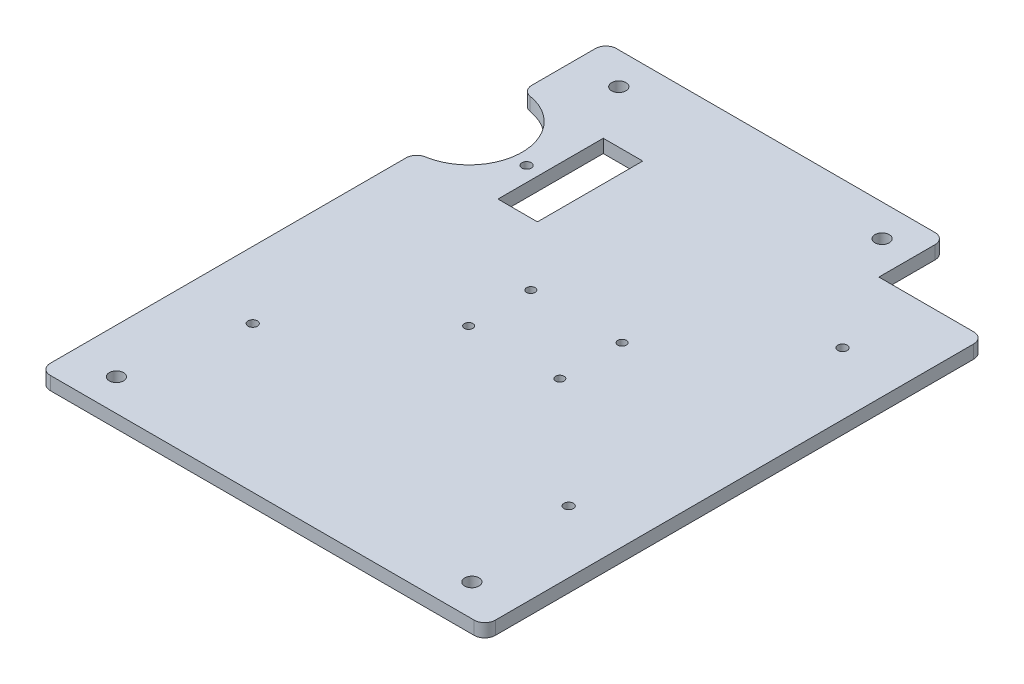
SolidWorks part; units mm, degrees
ref_plane "Front Plane" through (0, 0, 0) normal (0, 0, 1) x (1, 0, 0)
ref_plane "Top Plane" through (0, 0, 0) normal (0, 1, 0) x (1, 0, 0)
ref_plane "Right Plane" through (0, 0, 0) normal (1, 0, 0) x (0, 0, -1)
sketch "Sketch1" plane through (0, 0, 0) normal (0, 1, 0) x (1, 0, 0)
  line L0 (10.795, 128.8415) -> (96.52, 128.8415) construction
  line L1 (0, 136.525) -> (107.315, 136.525) construction
  line L2 (0, 136.525) -> (0, 0)
  line L3 (0, 0) -> (107.315, 0)
  line L4 (107.315, 136.525) -> (107.315, 0) construction
  line L5 (10.795, 7.6835) -> (96.52, 7.6835) construction
  line L6 (53.6575, 136.525) -> (53.6575, 128.8415) construction
  line L7 (0, 68.2625) -> (107.315, 68.2625) construction
  line L8 (53.6575, 7.6835) -> (53.6575, 0) construction
  line L9 (0, 136.525) -> (81.915, 136.525)
  line L10 (81.915, 136.525) -> (81.915, 120.4468)
  line L11 (81.915, 120.4468) -> (107.315, 120.4468)
  line L12 (107.315, 120.4468) -> (107.315, 0)
  circle A0 centre (10.795, 128.8415) radius 1.7272
  circle A2 centre (96.52, 7.6835) radius 1.7272
  circle A3 centre (10.795, 7.6835) radius 1.7272
  circle A4 centre (74.295, 128.8415) radius 1.7272
  dimension "D4" = 3.4544
  dimension "D1" = 107.315
  dimension "D2" = 136.525
  dimension "D3" = 85.725
  dimension "D5" = 7.6835
  dimension "D6" = 22.225
  dimension "D7" = 81.915
  dimension "D8" = 16.0782
extrude "Boss-Extrude1" add sketch "Sketch1" along normal blind 3.2004
sketch "Sketch2" plane through (0, 3.2004, 0) normal (0, 1, 0) x (1, 0, 0)
  line L0 (0, 136.525) -> (0, 0) construction
  line L3 (81.915, 136.525) -> (0, 136.525) construction
  line L4 (24.4475, 103.505) -> (0, 103.505) construction
  line L5 (29.21, 116.205) -> (19.685, 116.205)
  line L6 (29.21, 116.205) -> (29.21, 90.805)
  line L7 (29.21, 90.805) -> (19.685, 90.805)
  line L8 (19.685, 116.205) -> (19.685, 90.805)
  line L9 (24.4475, 116.205) -> (24.4475, 90.805) construction
  line L12 (0, 116.3304) -> (0, 90.6796)
  arc A0 (0, 116.3304) -> (0, 90.6796) centre (0, 103.505) cw
  dimension "D3" = 12.8254
  dimension "D1" = 33.02
  dimension "D4" = 24.4475
  dimension "D5" = 9.525
  dimension "D6" = 25.4
extrude "Cut-Extrude1" cut sketch "Sketch2" against normal up to surface (3.2004 mm away) up to face at (96.52, 0, -5.9563)
sketch "Sketch3" plane through (0, 3.2004, 0) normal (0, 1, 0) x (1, 0, 0)
  line L8 (53.6575, 136.525) -> (53.6575, 0) construction
  line L12 (0, 0) -> (107.315, 0) construction
  line L13 (0, 136.525) -> (107.315, 136.525) construction
  line L74 (92.3128, 101.2825) -> (92.3128, 35.2425) construction
  line L76 (16.1128, 35.2425) -> (16.1128, 101.2825) construction
  line L78 (92.3128, 68.2625) -> (16.1128, 68.2625) construction
  circle A0 centre (92.3128, 101.2825) radius 1.1303
  circle A1 centre (92.3128, 35.2425) radius 1.1303
  circle A2 centre (16.1128, 35.2425) radius 1.1303
  circle A3 centre (16.1128, 101.2825) radius 1.1303
  point P18 (53.6575, 68.2625)
  point P80 (54.2128, 68.2625)
  dimension "D7" = 2.2606
  dimension "D1" = 0.5553
  dimension "D5" = 76.2
  dimension "D6" = 66.04
extrude "Cut-Extrude2" cut sketch "Sketch3" against normal up to surface (3.2004 mm away) up to face at (48.9107, 0, -90.1192)
fillet "Fillet1" radius 2.54 7 edges at (0, 1.6002, -90.6796) (0, 1.6002, -116.3304) (0, 1.6002, 0) (107.315, 1.6002, 0) (107.315, 1.6002, -120.4468) (81.915, 1.6002, -136.525) (0, 1.6002, -136.525)
sketch "Sketch4" plane through (0, 3.2004, 0) normal (0, 1, 0) x (1, 0, 0)
  line L0 (64.6575, 68.2625) -> (42.6575, 68.2625) construction
  line L2 (53.6575, 136.525) -> (53.6575, 0) construction
  line L3 (64.6575, 75.7625) -> (64.6575, 60.7625) construction
  line L4 (42.6575, 75.7625) -> (42.6575, 60.7625) construction
  circle A0 centre (64.6575, 75.7625) radius 1.0249
  circle A1 centre (64.6575, 60.7625) radius 1.0249
  circle A2 centre (42.6575, 75.7625) radius 1.0249
  circle A3 centre (42.6575, 60.7625) radius 1.0249
  dimension "D3" = 2.0498
  dimension "D1" = 22
  dimension "D2" = 15
extrude "Cut-Extrude3" cut sketch "Sketch4" against normal up to surface (3.2004 mm away) up to face at (16.1128, 0, -102.4128)
